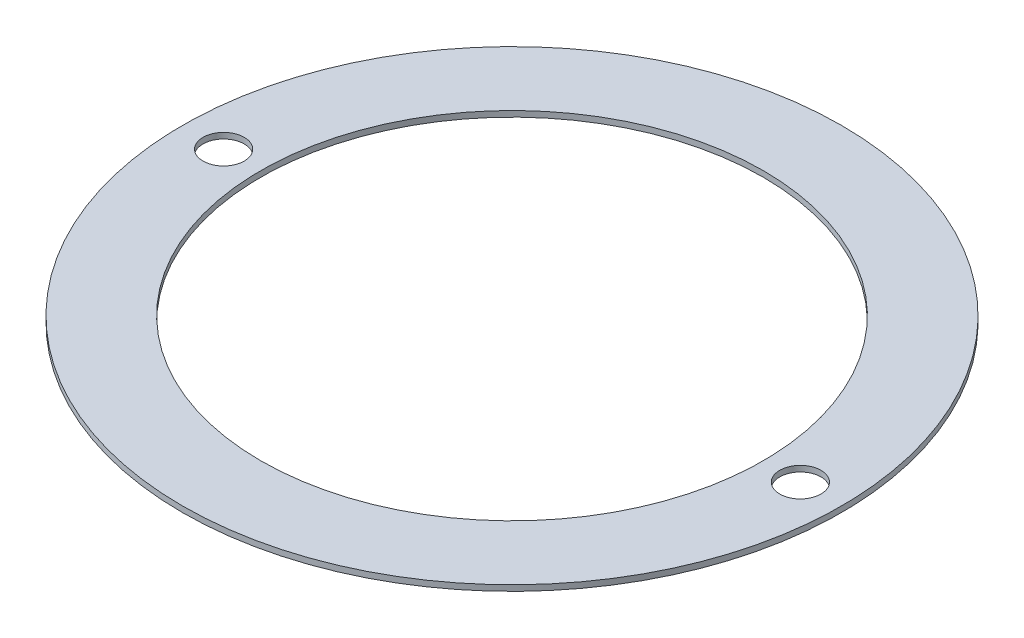
SolidWorks part; units mm, degrees
ref_plane "Front Plane" through (0, 0, 0) normal (0, 0, 1) x (1, 0, 0)
ref_plane "Top Plane" through (0, 0, 0) normal (0, 1, 0) x (1, 0, 0)
ref_plane "Right Plane" through (0, 0, 0) normal (1, 0, 0) x (0, 0, -1)
sketch "Sketch1" plane through (0, 0, 0) normal (0, 1, 0) x (1, 0, 0)
  circle A0 centre (0, 0) radius 8
  circle A1 centre (0, 0) radius 6.1
  dimension "D1" = 16
  dimension "D2" = 12.2
extrude "Boss-Extrude1" add sketch "Sketch1" along normal blind 0.14
hole_wizard "Ø1.0 (1) Diameter Hole1" positions "Sketch3" profile "Sketch4" hole size "Ø1.0" standard "DIN" end condition up to next
sketch "Sketch3" plane through (0, 0.14, 0) normal (0, 1, 0) x (1, 0, 0)
  circle A0 centre (0, 0) radius 7 construction
  point P5 (-7, 0)
  point P7 (7, 0)
  dimension "D1" = 14
sketch "Sketch4" plane through (-7, 0.14, 0) normal (1, 0, 0) x (0, 0, 1)
  line L0 (0, 0) -> (0, 0.14)
  line L1 (0, 0.14) -> (0.5, 0.14)
  line L2 (0.5, 0.14) -> (0.5, 0)
  line L5 (0.5, 0) -> (0, 0)
  line L11 (0, -6.35) -> (0, 107.95) construction
  dimension "Thru Hole Dia." = 1
  dimension "Thru Hole Depth" = 0.14
